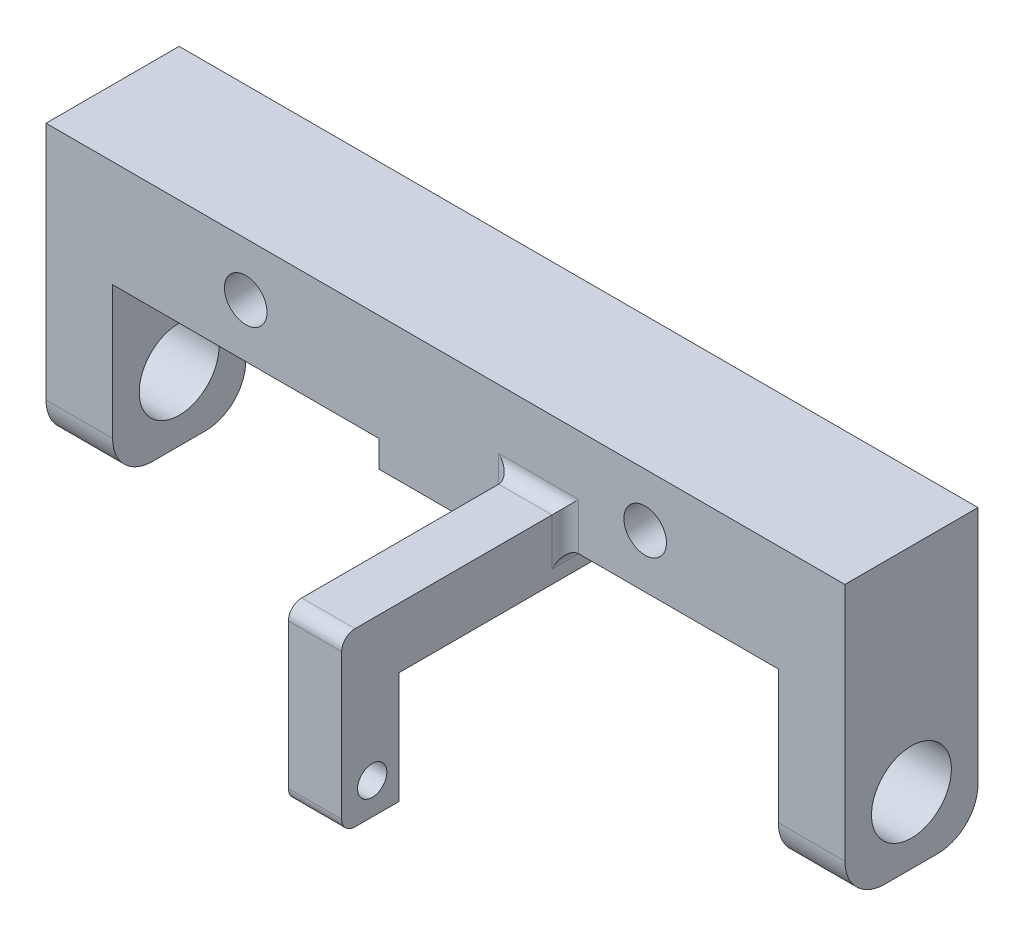
SolidWorks part; units mm, degrees
ref_plane "前视基准面" through (0, 0, 0) normal (0, 0, 1) x (1, 0, 0)
ref_plane "上视基准面" through (0, 0, 0) normal (0, 1, 0) x (1, 0, 0)
ref_plane "右视基准面" through (0, 0, 0) normal (1, 0, 0) x (0, 0, -1)
sketch "草图1" plane through (0, 0, 0) normal (0, 1, 0) x (1, 0, 0)
  line L1 (30, -5) -> (-30, -5)
  line L2 (30, -5) -> (30, 5)
  line L3 (30, 5) -> (-30, 5)
  line L4 (-30, -5) -> (-30, 5)
  line L5 (30, -5) -> (-30, 5) construction
  line L6 (30, 5) -> (-30, -5) construction
  point P0 (0, 0)
extrude "凸台-拉伸1" add sketch "草图1" along normal blind 8
sketch "草图2" plane through (30, 0, 0) normal (1, 0, 0) x (0, 0, -1)
  line L1 (-5, 8) -> (5, 8)
  line L2 (-5, 8) -> (-5, -13)
  line L3 (-5, -13) -> (5, -13)
  line L4 (5, 8) -> (5, -13)
  circle A0 centre (0, -8) radius 3
extrude "凸台-拉伸2" add sketch "草图2" against normal blind 5
mirror "镜向1" about plane through (0, 0, 0) normal (1, 0, 0) of "凸台-拉伸2"
fillet "圆角1" radius 3 4 edges at (-27.5, -13, -5) (-27.5, -13, 5) (27.5, -13, -5) (27.5, -13, 5)
ref_plane "基准面1" through (5, 0, 0) normal (-1, 0, 0) x (0, 0, 1)
sketch "草图3" plane through (5, 0, 0) normal (-1, 0, 0) x (0, 0, 1)
  line L0 (-8.5, -8) -> (-8.5, -2) construction
  line L1 (-6.5, -2) -> (17.5, -2)
  line L2 (-8.5, -8) -> (-6.5, -8) construction
  line L3 (-6.5, -8) -> (-6.5, -2)
  line L4 (-6.5, -8) -> (-6.5, -10.3764)
  line L5 (-6.5, -10.3764) -> (-10.8923, -10.3764)
  line L6 (-10.8923, -10.3764) -> (-10.8923, 2.5198)
  line L7 (-10.8923, 2.5198) -> (21.7929, 2.5198)
  line L8 (19.5, -8) -> (17.5, -8) construction
  line L9 (17.5, -8) -> (17.5, -2)
  line L10 (17.5, -8) -> (17.5, -10.3764)
  line L11 (17.5, -10.3764) -> (21.7929, -10.3764)
  line L12 (21.7929, -10.3764) -> (21.7929, 2.5198)
  circle A0 centre (0, -8) radius 3 construction
  circle A1 centre (0, -8) radius 3 construction
  circle A2 centre (-8.5, -8) radius 1.1
  circle A3 centre (19.5, -8) radius 1.1
extrude "凸台-拉伸3" add sketch "草图3" against normal blind 4
sketch "草图5" plane through (5, 0, 0) normal (-1, 0, 0) x (0, 0, 1)
  line L0 (5, 8) -> (5, -10) construction
  line L1 (-5, 0) -> (5, 0)
  line L2 (-5, 0) -> (-5, -2)
  line L3 (-5, -2) -> (5, -2)
  line L4 (5, 0) -> (5, -2)
  line L5 (-6.5, -2) -> (17.5, -2) construction
extrude "凸台-拉伸4" add sketch "草图5" along normal blind 10
fillet "圆角4" radius 1 11 edges at (9, 0, 0) (5, 0.2599, -5) (9, 1.2599, -5) (9, 1.2599, 5) (7, 2.5198, 21.7929) (7, -10.3764, 21.7929) (7, -10.3764, -10.8923) (7, 2.5198, -10.8923) (7, 2.5198, -5) (7, 2.5198, 5) (5, 0.2599, 5)
sketch "草图4" plane through (0, 0, 5) normal (0, 0, 1) x (1, 0, 0)
  circle A0 centre (-15, 4) radius 1.6
  circle A1 centre (15, 4) radius 1.6
extrude "切除-拉伸1" cut sketch "草图4" against normal through all both and the other way through all
